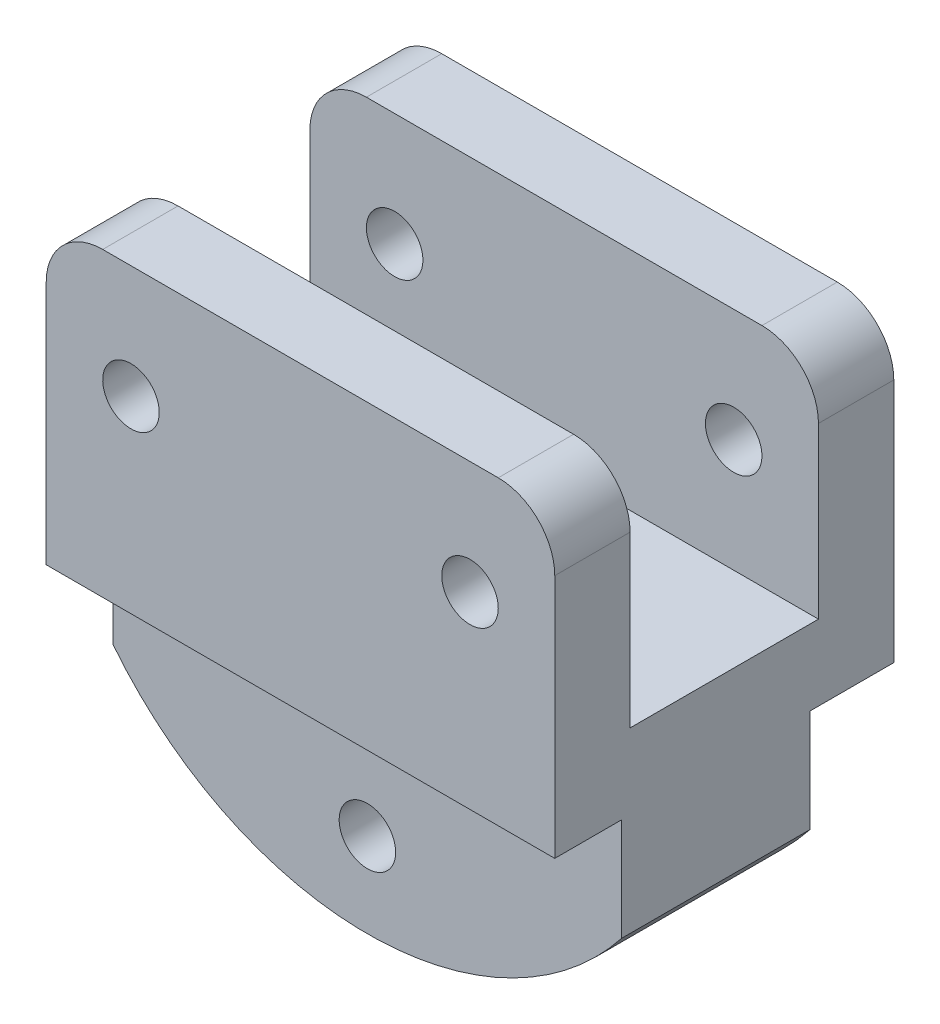
SolidWorks part; units mm, degrees
ref_plane "Front Plane" through (0, 0, 0) normal (0, 0, 1) x (1, 0, 0)
ref_plane "Top Plane" through (0, 0, 0) normal (0, 1, 0) x (1, 0, 0)
ref_plane "Right Plane" through (0, 0, 0) normal (1, 0, 0) x (0, 0, -1)
sketch "Sketch2" plane through (0, 0, 0) normal (0, 0, 1) x (1, 0, 0)
  line L0 (0, -6) -> (27, -6) construction
  line L1 (0, 0) -> (27, 0)
  line L2 (0, 0) -> (0, -12)
  line L4 (27, 0) -> (27, -12)
  line L5 (13.5, 0) -> (13.5, -6) construction
  line L6 (24, -6) -> (27, -6)
  line L7 (3, -6) -> (0, -6)
  line L8 (6, -6) -> (21, -6)
  line L11 (0, -12) -> (0, -16)
  line L12 (0, -16) -> (27, -16)
  line L13 (27, -12) -> (27, -16)
  circle A0 centre (4.5, -6) radius 1.5
  circle A1 centre (22.5, -6) radius 1.5
  dimension "D1" = 3
  dimension "D2" = 3
  dimension "D3" = 3
  dimension "D4" = 3
  dimension "D5" = 15
  dimension "D6" = 10
  dimension "D7" = 4
extrude "Boss-Extrude1" add sketch "Sketch2" along normal blind 18
sketch "Sketch3" plane through (0, 0, 0) normal (-1, 0, 0) x (0, 0, 1)
  line L0 (18, 0) -> (0, 0) construction
  line L1 (4, 0) -> (14, 0)
  line L2 (4, 0) -> (4, -12)
  line L3 (4, -12) -> (14, -12)
  line L4 (14, 0) -> (14, -12)
  line L5 (0, 0) -> (0, -16) construction
  line L6 (18, 0) -> (18, -16) construction
  line L7 (18, -16) -> (0, -16) construction
  dimension "D1" = 4
  dimension "D2" = 4
  dimension "D3" = 4
extrude "Cut-Extrude1" cut sketch "Sketch3" against normal blind 32 contours L2 L1 L4 L3
sketch "Sketch4" plane through (0, -16, 0) normal (0, -1, 0) x (1, 0, 0)
  line L0 (0, 18) -> (0, 0) construction
  line L1 (0, 14.4473) -> (27, 14.4473)
  line L2 (0, 14.4473) -> (0, 4.4473)
  line L3 (0, 4.4473) -> (27, 4.4473)
  line L4 (27, 14.4473) -> (27, 4.4473)
  line L5 (27, 18) -> (27, 0) construction
  line L6 (0, 9.4473) -> (27, 9.4473)
  line M4 (27, 0) -> (27, 18)
  line M6 (0, 18) -> (0, 0)
  dimension "D1" = 5
sketch "Sketch7" plane through (0, -16, 0) normal (0, -1, 0) x (1, 0, 0)
extrude "Boss-Extrude3" add sketch "Sketch4" along normal blind 12 contours L6 L4 L1 M6 | L6 L2 L3 M4
sketch "Sketch8" plane through (0, 0, 4.4473) normal (0, 0, -1) x (-1, 0, 0)
  line L0 (-13.5, -28) -> (-13.5, -7.9683) construction
  line L1 (0, -28) -> (-27, -28) construction
  line L2 (-13.5, -25) -> (-13.5, -28)
  line L3 (-27, -21.451) -> (-27, -28)
  line L4 (-27, -28) -> (-27, -16) construction
  line L5 (-27, -28) -> (0, -28)
  line L6 (0, -28) -> (0, -21.451)
  line L7 (0, -28) -> (0, -16) construction
  circle A0 centre (-13.5, -23.5) radius 1.5
  arc A1 (-27, -21.451) -> (0, -21.451) centre (-13.5, -10.8017) ccw
  line M5 (-27, -16) -> (-27, -28)
  line M6 (-27, -28) -> (0, -28)
  line M7 (0, -28) -> (0, -16)
  dimension "D1" = 3
  dimension "D2" = 3
extrude "Cut-Extrude3" cut sketch "Sketch8" against normal blind 12 contours A0 L0 | A1 L2 M5 M6 | A1 L2 M6 M7
fillet "Fillet1" radius 3 1 edges at (0, 0, 2)
fillet "Fillet2" radius 3 1 edges at (27, 0, 2)
fillet "Fillet3" radius 3 1 edges at (0, 0, 16)
fillet "Fillet4" radius 3 1 edges at (27, 0, 16)
